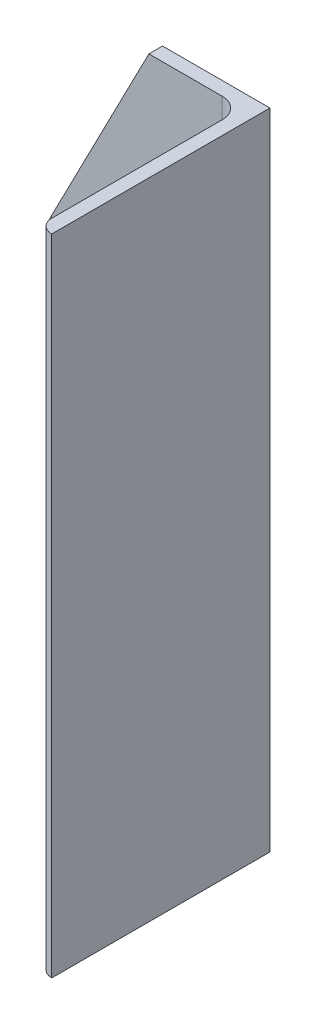
SolidWorks part; units mm, degrees
ref_plane "Alzado" through (0, 0, 0) normal (0, 0, 1) x (1, 0, 0)
ref_plane "Planta" through (0, 0, 0) normal (0, 1, 0) x (1, 0, 0)
ref_plane "Vista lateral" through (0, 0, 0) normal (1, 0, 0) x (0, 0, -1)
sketch "Croquis1" plane through (0, 0, 0) normal (0, 0, 1) x (1, 0, 0)
  line L0 (0, 0) -> (0, 150)
  dimension "D1" = 150
other "Hierro angular 2 X 2 X 0.125(1)"
ref_plane "Plano1" through (0, 0, 0) normal (0, 1, 0) x (-1, 0, 0)
sketch "Sketch1" plane through (0, 0, 0) normal (0, 1, 0) x (-1, 0, 0)
  line L0 (0, 0) -> (0, 50.8)
  line L1 (0, 50.8) -> (0.0051, 50.8)
  line L2 (3.175, 47.6301) -> (3.175, 7.9375)
  line L3 (7.9375, 3.175) -> (47.6301, 3.175)
  line L4 (50.8, 0.0051) -> (50.8, 0)
  line L5 (50.8, 0) -> (0, 0)
  arc A0 (50.8, 0.0051) -> (47.6301, 3.175) centre (47.6301, 0.0051) ccw
  arc A1 (0.0051, 50.8) -> (3.175, 47.6301) centre (0.0051, 47.6301) cw
  arc A2 (7.9375, 3.175) -> (3.175, 7.9375) centre (7.9375, 7.9375) cw
  point P10 (25.4, 0)
  point P14 (0, 25.4)
  point P15 (3.175, 25.4)
  point P16 (25.4, 3.175)
  point P17 (3.175, 50.8)
  point P18 (50.8, 3.175)
  point P19 (0, 0)
  dimension "D2" = 0.0051
  dimension "Radius_1" = 4.7625
  dimension "D1" = 3.175
  dimension "H_leg" = 50.8
sketch "Croquis3" plane through (0, 0, 0) normal (0, 0, -1) x (-1, 0, 0)
  line L0 (50.8, 100) -> (0, 100) construction
  line L1 (50.8, 150) -> (50.8, 0) construction
  line L2 (0, 0) -> (0, 150) construction
  line L3 (0, 0) -> (50.8, 0) construction
  line L4 (25, 100) -> (25, 150) construction
  line L5 (0, 150) -> (50.8, 150) construction
  line L6 (50.8, 100) -> (25, 150)
  line L7 (25, 150) -> (50.8, 150)
  line L8 (50.8, 150) -> (50.8, 100)
  dimension "D1" = 100
  dimension "D2" = 25
extrude "Cortar-Extruir1" cut sketch "Croquis3" against normal blind 10
sketch "Croquis4" plane through (0, 0, 0) normal (0, 0, -1) x (-1, 0, 0)
  line L0 (50.8, 100) -> (50.8, 0) construction
  line L1 (45.4, 9.88) -> (17.9, 9.88) construction
  line L2 (45.4, 9.88) -> (45.4, 90.13) construction
  line L3 (45.4, 90.13) -> (17.9, 90.13) construction
  line L4 (17.9, 9.88) -> (17.9, 90.13) construction
  line L5 (0, 0) -> (50.8, 0) construction
  circle A0 centre (45.4, 9.88) radius 2.5
  circle A1 centre (17.9, 9.88) radius 2.5
  circle A2 centre (45.4, 90.13) radius 2.5
  circle A3 centre (17.9, 90.13) radius 2.5
  dimension "D5" = 5
  dimension "D1" = 5.4
  dimension "D2" = 9.88
  dimension "D3" = 27.5
  dimension "D4" = 80.25
extrude "Cortar-Extruir2" cut sketch "Croquis4" against normal up to surface (3.175 mm away) up to face at (-27.227, 81.2287, 3.175)
